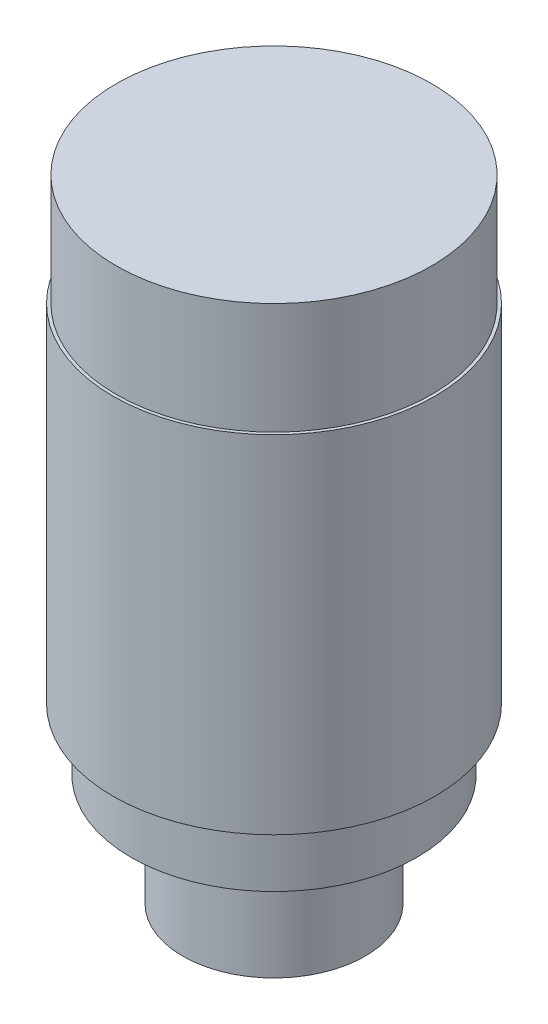
SolidWorks part; units mm, degrees
ref_plane "前视基准面" through (0, 0, 0) normal (0, 0, 1) x (1, 0, 0)
ref_plane "上视基准面" through (0, 0, 0) normal (0, 1, 0) x (1, 0, 0)
ref_plane "右视基准面" through (0, 0, 0) normal (1, 0, 0) x (0, 0, -1)
sketch "Sketch1" plane through (0, 0, 0) normal (0, 1, 0) x (1, 0, 0)
  circle A0 centre (0, 0) radius 14.75
  dimension "D1" = 29.5
extrude "Boss-Extrude1" add sketch "Sketch1" along normal blind 18
sketch "Sketch2" plane through (0, 18, 0) normal (0, 1, 0) x (1, 0, 0)
  circle A0 centre (0, 0) radius 23.1
  dimension "D1" = 46.2
extrude "Boss-Extrude2" add sketch "Sketch2" along normal blind 10
sketch "Sketch3" plane through (0, 28, 0) normal (0, 1, 0) x (1, 0, 0)
  circle A0 centre (0, 0) radius 26
  dimension "D1" = 52
extrude "Boss-Extrude3" add sketch "Sketch3" along normal blind 74
sketch "Sketch4" plane through (0, 102, 0) normal (0, 1, 0) x (1, 0, 0)
  circle A0 centre (0, 0) radius 26
  circle A1 centre (0, 0) radius 26 construction
  circle A2 centre (0, 0) radius 25.5
  dimension "D1" = 51
extrude "Cut-Extrude1" cut sketch "Sketch4" against normal blind 18
